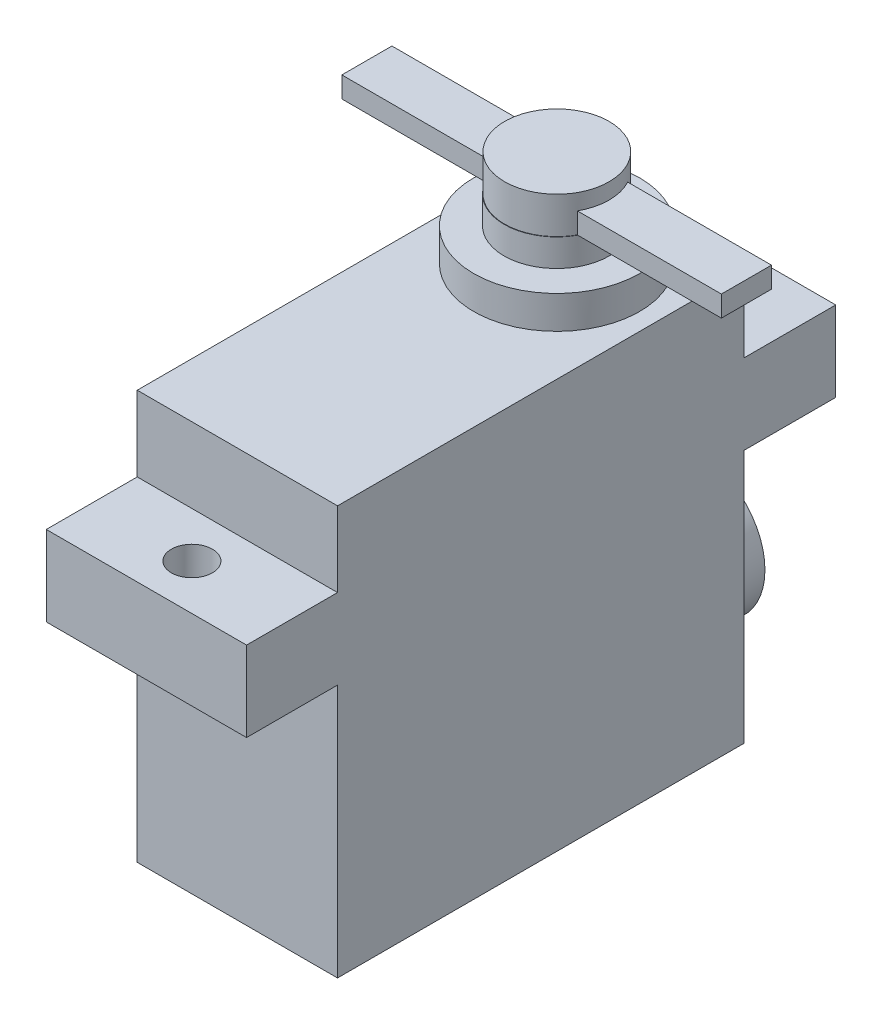
SolidWorks part; units mm, degrees
ref_plane "Front Plane" through (0, 0, 0) normal (0, 0, 1) x (1, 0, 0)
ref_plane "Top Plane" through (0, 0, 0) normal (0, 1, 0) x (1, 0, 0)
ref_plane "Right Plane" through (0, 0, 0) normal (1, 0, 0) x (0, 0, -1)
sketch "Sketch1" plane through (0, 0, 0) normal (0, 1, 0) x (1, 0, 0)
  line L1 (0, 0) -> (15.24, 0)
  line L2 (0, 0) -> (0, 30.9118)
  line L3 (0, 30.9118) -> (15.24, 30.9118)
  line L4 (15.24, 0) -> (15.24, 30.9118)
  dimension "D1" = 15.24
  dimension "D2" = 30.9118
extrude "Boss-Extrude1" add sketch "Sketch1" along normal blind 31.115
sketch "Sketch2" plane through (0, 0, 0) normal (0, 0, 1) x (1, 0, 0)
  line L0 (0, 31.115) -> (0, 0) construction
  line L1 (0, 25.4) -> (15.24, 25.4)
  line L2 (0, 25.4) -> (0, 19.304)
  line L3 (0, 19.304) -> (15.24, 19.304)
  line L4 (15.24, 25.4) -> (15.24, 19.304)
  line L5 (15.24, 31.115) -> (15.24, 0) construction
  line L6 (0, 0) -> (15.24, 0) construction
  dimension "D1" = 19.304
  dimension "D2" = 6.096
extrude "Boss-Extrude2" add sketch "Sketch2" along normal blind 6.9215 and the other way blind 37.9095
sketch "Sketch3" plane through (0, 0, -30.9118) normal (0, 0, -1) x (-1, 0, 0)
  line L0 (-15.24, 0) -> (0, 0) construction
  circle A0 centre (-7.62, 8.2804) radius 5.2705
  dimension "D1" = 10.541
  dimension "D2" = 8.2804
extrude "Boss-Extrude3" add sketch "Sketch3" along normal blind 3.9624
sketch "Sketch4" plane through (0, 31.115, 0) normal (0, 1, 0) x (1, 0, 0)
  line L0 (15.24, 30.9118) -> (0, 30.9118) construction
  circle A0 centre (7.62, 24.2951) radius 6.3119
  dimension "D1" = 12.6238
  dimension "D2" = 6.6167
extrude "Boss-Extrude4" add sketch "Sketch4" along normal blind 2.5019
sketch "Sketch8" plane through (0, 25.4, 0) normal (0, 1, 0) x (1, 0, 0)
  circle A0 centre (7.62, -3.4608) radius 1.5621
  dimension "D1" = 3.1242
extrude "Cut-Extrude1" cut sketch "Sketch8" against normal up to next
sketch "Sketch9" plane through (0, 25.4, 0) normal (0, 1, 0) x (1, 0, 0)
  circle A0 centre (7.62, 34.4107) radius 1.5621
  dimension "D1" = 3.1242
extrude "Cut-Extrude2" cut sketch "Sketch9" against normal up to next
sketch "Sketch10" plane through (0, 33.6169, 0) normal (0, 1, 0) x (1, 0, 0)
  circle A0 centre (7.62, 24.2951) radius 3.9942
  circle A8 centre (7.62, 24.2951) radius 6.3119 construction
  dimension "D1" = 7.9883
extrude "Boss-Extrude5" add sketch "Sketch10" along normal blind 2.0828
sketch "Sketch11" plane through (0, 35.6997, 0) normal (0, 1, 0) x (1, 0, 0)
  line L0 (3.6258, 24.2951) -> (11.6141, 24.2951) construction
  line L1 (7.62, 26.2001) -> (7.62, 22.3901)
  line L2 (7.62, 26.2001) -> (7.62, 22.3901)
  line L3 (7.62, 26.2001) -> (22.0599, 26.2001)
  line L4 (7.62, 22.3901) -> (22.0599, 22.3901)
  line L5 (22.0599, 26.2001) -> (22.0599, 22.3901)
  line L6 (7.62, 26.2001) -> (7.62, 22.3901)
  line L7 (7.62, 26.2001) -> (-6.8199, 26.2001)
  line L8 (7.62, 22.3901) -> (-6.8199, 22.3901)
  line L9 (-6.8199, 26.2001) -> (-6.8199, 22.3901)
  circle A0 centre (7.62, 24.2951) radius 3.9941 construction
  circle A1 centre (7.62, 24.2951) radius 3.9941 construction
  circle M4 centre (7.62, 24.2951) radius 3.9942
  dimension "D1" = 1.905
  dimension "D2" = 1.905
  dimension "D3" = 14.4399
  dimension "D4" = 14.4399
extrude "Boss-Extrude6" add sketch "Sketch11" along normal blind 1.5875 contours L7 L9 L8 M4 | L0 L1 L7 M4 | L0 L8 L6 M4 | L1 L0 L3 M4 | L0 L6 L4 M4 | L5 L3 L4 M4
sketch "Sketch12" plane through (0, 35.6997, 0) normal (0, 1, 0) x (1, 0, 0)
  circle A0 centre (7.6196, 24.3125) radius 3.9768
extrude "Boss-Extrude7" add sketch "Sketch12" along normal blind 2.794
